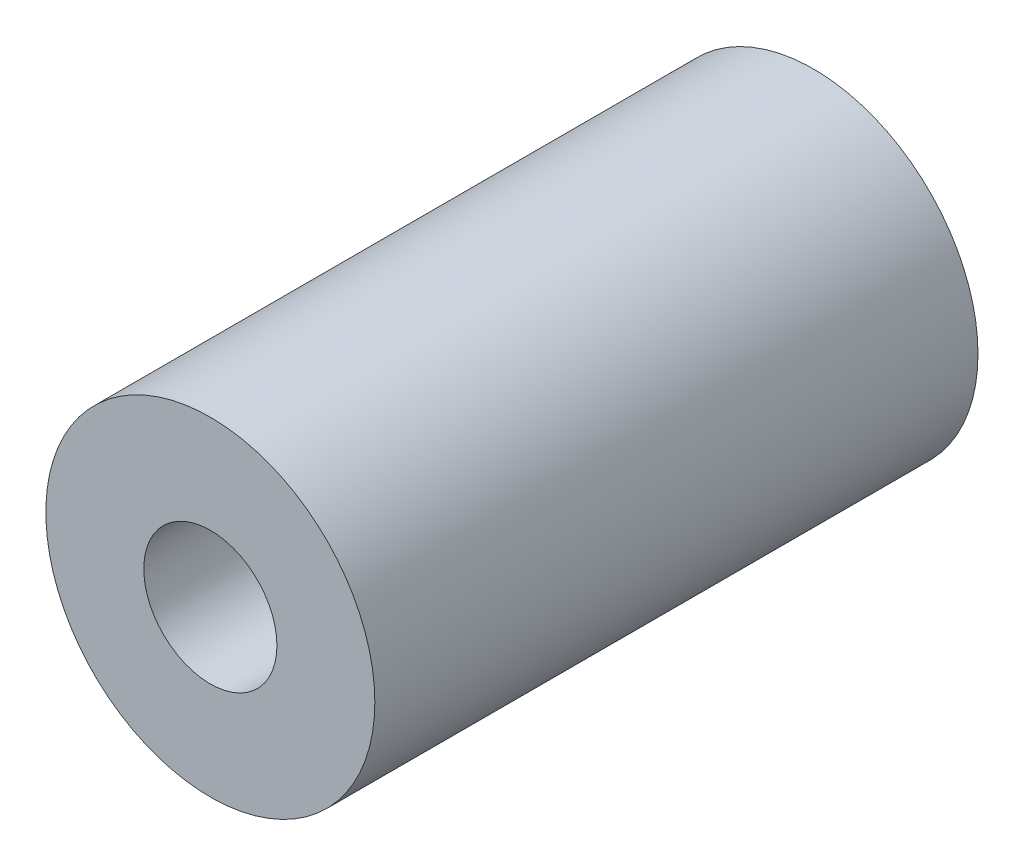
SolidWorks part; units mm, degrees
ref_plane "Front Plane" through (0, 0, 0) normal (0, 0, 1) x (1, 0, 0)
ref_plane "Top Plane" through (0, 0, 0) normal (0, 1, 0) x (1, 0, 0)
ref_plane "Right Plane" through (0, 0, 0) normal (1, 0, 0) x (0, 0, -1)
sketch "Sketch1" plane through (0, 0, 0) normal (0, 1, 0) x (1, 0, 0)
  line L0 (2.125, -3.75) -> (5.25, -3.75)
  line L1 (5.25, -3.75) -> (5.25, 0)
  line L2 (5.25, 0) -> (2.125, 0)
  line L3 (2.125, 0) -> (2.125, -3.75)
  line L4 (0, 0) -> (0, -3.75) construction
  dimension "D1" = 2.125
  dimension "D2" = 5.25
  dimension "D3" = 3.75
revolve "Revolve1" add sketch "Sketch1" angle 360 about L4
sketch "Sketch2" plane through (0, 0, 3.75) normal (0, 0, 1) x (1, 0, 0)
  circle A0 centre (0, 0) radius 2.125
  circle A1 centre (0, 0) radius 5.25
  circle A2 centre (0, 0) radius 5.25 construction
  dimension "D1" = 4.25
extrude "Boss-Extrude1" add sketch "Sketch2" along normal blind 16
sketch "Sketch3" plane through (0, 0, 0) normal (0, 0, -1) x (-1, 0, 0)
  circle A0 centre (0, 0) radius 3
  circle A1 centre (0, 0) radius 5.25
  circle A2 centre (0, 0) radius 5.25
  dimension "D2" = 6
  dimension "D1" = 0
extrude "Cut-Extrude1" cut sketch "Sketch3" against normal blind 0.5
